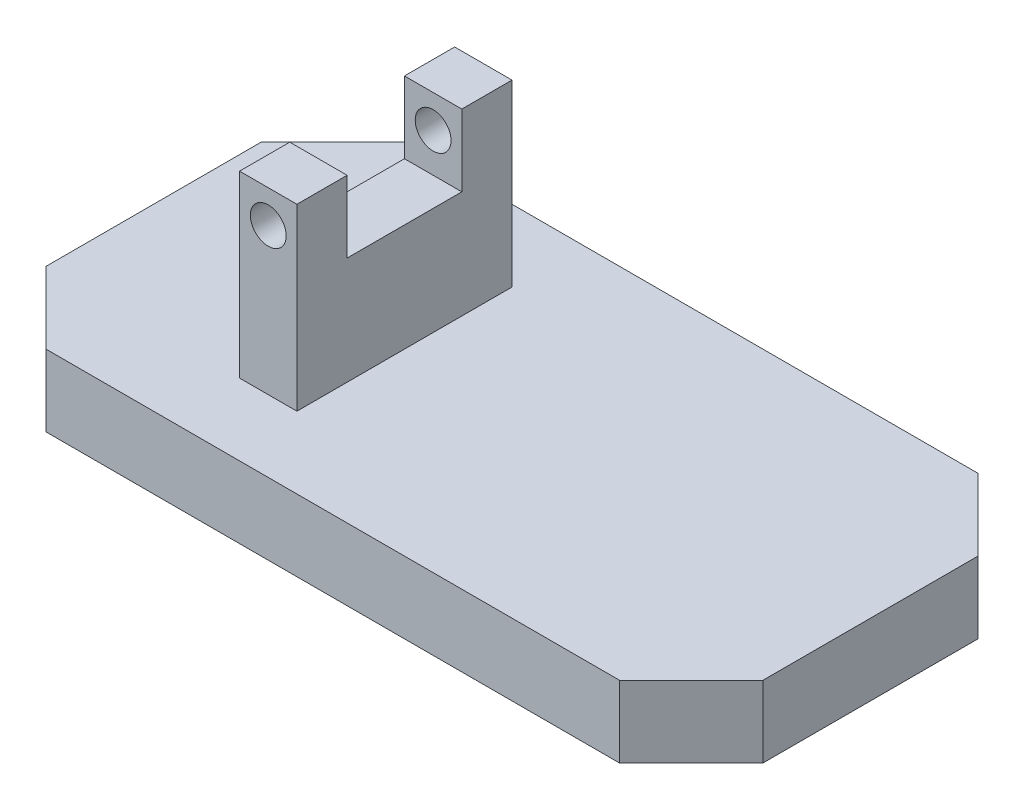
SolidWorks part; units mm, degrees
ref_plane "Front Plane" through (0, 0, 0) normal (0, 0, 1) x (1, 0, 0)
ref_plane "Top Plane" through (0, 0, 0) normal (0, 1, 0) x (1, 0, 0)
ref_plane "Right Plane" through (0, 0, 0) normal (1, 0, 0) x (0, 0, -1)
sketch "Sketch1" plane through (0, 0, 0) normal (0, 1, 0) x (1, 0, 0)
  line L1 (-50, 25) -> (50, 25)
  line L2 (-50, 25) -> (-50, -25)
  line L3 (-50, -25) -> (50, -25)
  line L4 (50, 25) -> (50, -25)
  dimension "D1" = 50
  dimension "D2" = 100
  dimension "D3" = 50
  dimension "D4" = 25
extrude "Boss-Extrude1" add sketch "Sketch1" along normal blind 10
chamfer "Chamfer1" distance 10 angle 45 4 edges at (-50, 5, -25) (-50, 5, 25) (50, 5, -25) (50, 5, 25)
sketch "Sketch2" plane through (0, 10, 0) normal (0, 1, 0) x (1, 0, 0)
  line L1 (-23, 15) -> (-15, 15)
  line L2 (-23, 15) -> (-23, -15)
  line L3 (-23, -15) -> (-15, -15)
  line L4 (-15, 15) -> (-15, -15)
  dimension "D1" = 8
  dimension "D2" = 15
  dimension "D3" = 15
  dimension "D4" = 15
extrude "Boss-Extrude2" add sketch "Sketch2" along normal blind 25
sketch "Sketch3" plane through (0, 35, 0) normal (0, 1, 0) x (1, 0, 0)
  line L1 (-30.248, 8) -> (-5.9227, 8)
  line L2 (-30.248, 8) -> (-30.248, -8)
  line L3 (-30.248, -8) -> (-5.9227, -8)
  line L4 (-5.9227, 8) -> (-5.9227, -8)
  dimension "D1" = 8
  dimension "D2" = 8
extrude "Cut-Extrude1" cut sketch "Sketch3" against normal blind 10
sketch "Sketch4" plane through (0, 0, 15) normal (0, 0, 1) x (1, 0, 0)
  line L0 (-15, 35) -> (-15, 10) construction
  circle A0 centre (-19, 30.4286) radius 2.5
  dimension "D1" = 5
  dimension "D2" = 4
extrude "Cut-Extrude2" cut sketch "Sketch4" against normal blind 42
